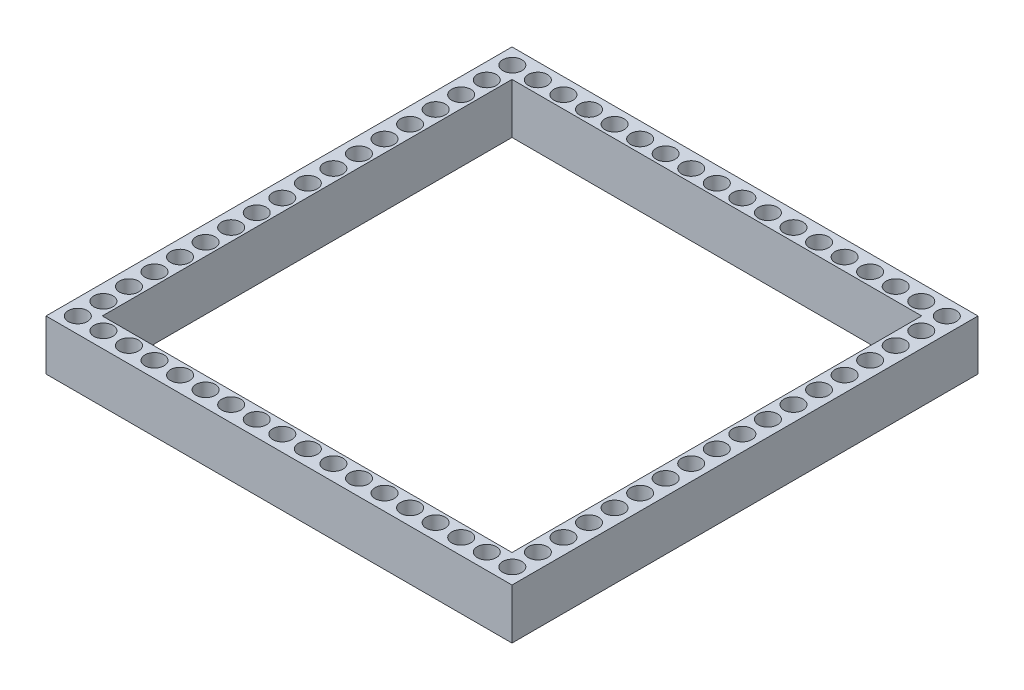
SolidWorks part; units mm, degrees
material "PP Copolymer"
ref_plane "Front Plane" through (0, 0, 0) normal (0, 0, 1) x (1, 0, 0)
ref_plane "Top Plane" through (0, 0, 0) normal (0, 1, 0) x (1, 0, 0)
ref_plane "Right Plane" through (0, 0, 0) normal (1, 0, 0) x (0, 0, -1)
sketch "Sketch2" plane through (0, 0, 0) normal (0, 1, 0) x (1, 0, 0)
  line L1 (-23.1554, 23.1554) -> (23.1554, 23.1554)
  line L2 (-23.1554, 23.1554) -> (-23.1554, -23.1554)
  line L3 (-23.1554, -23.1554) -> (23.1554, -23.1554)
  line L4 (23.1554, 23.1554) -> (23.1554, -23.1554)
  line L5 (-23.1554, 23.1554) -> (23.1554, -23.1554) construction
  line L6 (-23.1554, -23.1554) -> (23.1554, 23.1554) construction
  line L7 (-20.3586, 20.3586) -> (20.3586, 20.3586)
  line L8 (-20.3586, 20.3586) -> (-20.3586, -20.3586)
  line L9 (-20.3586, -20.3586) -> (20.3586, -20.3586)
  line L10 (20.3586, 20.3586) -> (20.3586, -20.3586)
  line L11 (-20.3586, 20.3586) -> (20.3586, -20.3586) construction
  line L12 (-20.3586, -20.3586) -> (20.3586, 20.3586) construction
  point P0 (0, 0)
  point P6 (0, 0)
  dimension "D1" = 46.3108
  dimension "D2" = 46.3108
  dimension "D3" = 40.7172
  dimension "D4" = 40.7172
extrude "Boss-Extrude1" add sketch "Sketch2" along normal blind 5
sketch "Sketch1" plane through (0, 0, 0) normal (0, 1, 0) x (1, 0, 0)
  circle A47 centre (-21.5644, 21.5964) radius 0.95
  circle A62 centre (-19.0244, 21.5964) radius 0.95
  circle A71 centre (-21.5644, 19.0564) radius 0.95
  circle A72 centre (-16.4844, 21.5964) radius 0.95
  circle A73 centre (-13.9444, 21.5964) radius 0.95
  circle A74 centre (-11.4044, 21.5964) radius 0.95
  circle A75 centre (-8.8644, 21.5964) radius 0.95
  circle A76 centre (-6.3244, 21.5964) radius 0.95
  circle A77 centre (-3.7844, 21.5964) radius 0.95
  circle A78 centre (-1.2444, 21.5964) radius 0.95
  circle A79 centre (1.2956, 21.5964) radius 0.95
  circle A80 centre (3.8356, 21.5964) radius 0.95
  circle A81 centre (6.3756, 21.5964) radius 0.95
  circle A82 centre (8.9156, 21.5964) radius 0.95
  circle A83 centre (11.4556, 21.5964) radius 0.95
  circle A84 centre (13.9956, 21.5964) radius 0.95
  circle A85 centre (16.5356, 21.5964) radius 0.95
  circle A86 centre (19.0756, 21.5964) radius 0.95
  circle A87 centre (21.6156, 21.5964) radius 0.95
  circle A88 centre (-21.5644, 16.5164) radius 0.95
  circle A89 centre (-21.5644, 13.9764) radius 0.95
  circle A90 centre (-21.5644, 11.4364) radius 0.95
  circle A91 centre (-21.5644, 8.8964) radius 0.95
  circle A92 centre (-21.5644, 6.3564) radius 0.95
  circle A93 centre (-21.5644, 3.8164) radius 0.95
  circle A94 centre (-21.5644, 1.2764) radius 0.95
  circle A95 centre (-21.5644, -1.2636) radius 0.95
  circle A96 centre (-21.5644, -3.8036) radius 0.95
  circle A97 centre (-21.5644, -6.3436) radius 0.95
  circle A98 centre (-21.5644, -8.8836) radius 0.95
  circle A99 centre (-21.5644, -11.4236) radius 0.95
  circle A100 centre (-21.5644, -13.9636) radius 0.95
  circle A101 centre (-21.5644, -16.5036) radius 0.95
  circle A102 centre (-21.5644, -19.0436) radius 0.95
  circle A103 centre (-21.5644, -21.5836) radius 0.95
  circle A104 centre (-19.0244, -21.5836) radius 0.95
  circle A105 centre (-16.4844, -21.5836) radius 0.95
  circle A106 centre (-13.9444, -21.5836) radius 0.95
  circle A107 centre (-11.4044, -21.5836) radius 0.95
  circle A108 centre (-8.8644, -21.5836) radius 0.95
  circle A109 centre (-6.3244, -21.5836) radius 0.95
  circle A110 centre (-3.7844, -21.5836) radius 0.95
  circle A111 centre (-1.2444, -21.5836) radius 0.95
  circle A112 centre (1.2956, -21.5836) radius 0.95
  circle A113 centre (3.8356, -21.5836) radius 0.95
  circle A114 centre (6.3756, -21.5836) radius 0.95
  circle A115 centre (8.9156, -21.5836) radius 0.95
  circle A116 centre (11.4556, -21.5836) radius 0.95
  circle A117 centre (13.9956, -21.5836) radius 0.95
  circle A118 centre (16.5356, -21.5836) radius 0.95
  circle A119 centre (19.0756, -21.5836) radius 0.95
  circle A120 centre (21.6156, -21.5836) radius 0.95
  circle A121 centre (21.6156, 19.0564) radius 0.95
  circle A122 centre (21.6156, 16.5164) radius 0.95
  circle A123 centre (21.6156, 11.4364) radius 0.95
  circle A124 centre (21.6156, 8.8964) radius 0.95
  circle A125 centre (21.6156, 6.3564) radius 0.95
  circle A126 centre (21.6156, 3.8164) radius 0.95
  circle A127 centre (21.6156, 1.2764) radius 0.95
  circle A128 centre (21.6156, -1.2636) radius 0.95
  circle A129 centre (21.6156, -3.8036) radius 0.95
  circle A130 centre (21.6156, -6.3436) radius 0.95
  circle A131 centre (21.6156, -8.8836) radius 0.95
  circle A132 centre (21.6156, -11.4236) radius 0.95
  circle A133 centre (21.6156, -13.9636) radius 0.95
  circle A134 centre (21.6156, -16.5036) radius 0.95
  circle A135 centre (21.6156, -19.0436) radius 0.95
  circle A136 centre (21.6156, 13.9764) radius 0.95
  point P0 (-3.6554, 3.6554)
  point P1 (-15.8054, 16.4389)
extrude "Cut-Extrude1" cut sketch "Sketch1" along normal through all
